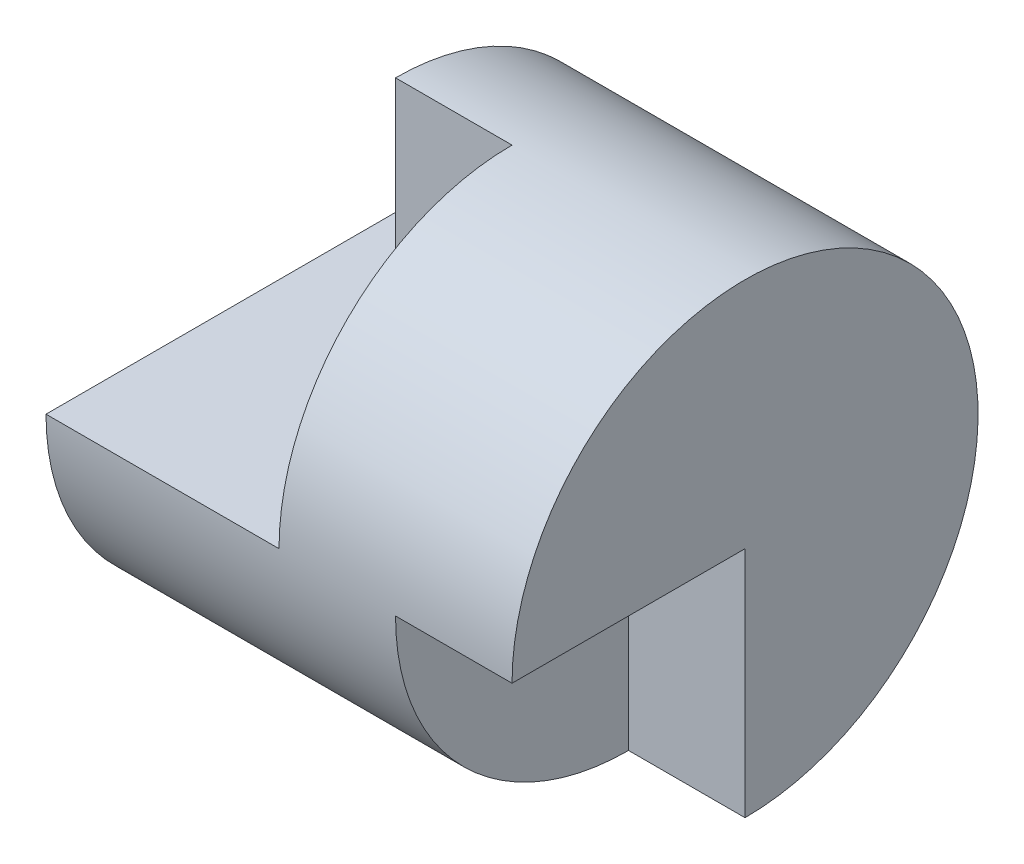
SolidWorks part; units mm, degrees
ref_plane "Front Plane" through (0, 0, 0) normal (0, 0, 1) x (1, 0, 0)
ref_plane "Top Plane" through (0, 0, 0) normal (0, 1, 0) x (1, 0, 0)
ref_plane "Right Plane" through (0, 0, 0) normal (1, 0, 0) x (0, 0, -1)
sketch "Sketch5" plane through (0, 0, 0) normal (0, 0, 1) x (1, 0, 0)
  line L0 (0, 0) -> (4, 0)
  dimension "D1" = 4
revolve "Revolve-Thin2" add sketch "Sketch5" angle 360 about L0 wall 2
sketch "Sketch6" plane through (0, 0, 0) normal (0, 0, 1) x (1, 0, 0)
  line L1 (0, 2) -> (1, 2)
  line L2 (0, 2) -> (0, 0)
  line L3 (0, 0) -> (1, 0)
  line L4 (1, 2) -> (1, 0)
  line L5 (4, 2) -> (3, 2)
  line L6 (4, 2) -> (4, 0)
  line L7 (4, 0) -> (3, 0)
  line L8 (3, 2) -> (3, 0)
  dimension "D1" = 1
  dimension "D2" = 1
  dimension "D3" = 2
  dimension "D4" = 2
extrude "Cut-Extrude5" cut sketch "Sketch6" against normal blind 11 contours L5 L8 L7 L6 | L4 L1 L2 L3
sketch "Sketch8" plane through (0, 0, 0) normal (0, 0, -1) x (-1, 0, 0)
  line L0 (0, 0) -> (-1, 0) construction
  line L1 (0, 2) -> (-0.5, 2)
  line L2 (0, 2) -> (0, 0)
  line L3 (0, 0) -> (-0.5, 0)
  line L4 (-0.5, 2) -> (-0.5, 0)
extrude "Cut-Extrude7" cut sketch "Sketch8" against normal blind 10
sketch "Sketch9" plane through (0, 0, 0) normal (0, 0, -1) x (-1, 0, 0)
  line L0 (-1, 2) -> (-3, 2) construction
  line L5 (-0.5, 0) -> (-2, 0)
  line L6 (-0.5, 0) -> (-0.5, 2)
  line L7 (-0.5, 2) -> (-2, 2)
  line L8 (-2, 0) -> (-2, 2)
  line L9 (-4, 2) -> (-4, 0) construction
  dimension "D1" = 2
extrude "Cut-Extrude8" cut sketch "Sketch9" against normal blind 10
sketch "Sketch10" plane through (4, 0, 0) normal (1, 0, 0) x (0, 0, -1)
  line L0 (2, 0) -> (-0.035, 0)
  line L1 (-0.035, 0) -> (0, 2)
  arc A0 (0, 2) -> (2, 0) centre (0, 0) cw
extrude "Boss-Extrude1" add sketch "Sketch10" against normal blind 1
sketch "Sketch12" plane through (4, 0, 0) normal (1, 0, 0) x (0, 0, -1)
  line L0 (0, 0) -> (-2.1336, 0)
  line L1 (-2.1336, 0) -> (-2.1336, -2.3246)
  line L2 (-2.1336, -2.3246) -> (0, -2.3246)
  line L3 (0, -2.3246) -> (0, 0)
extrude "Cut-Extrude9" cut sketch "Sketch12" against normal blind 1
